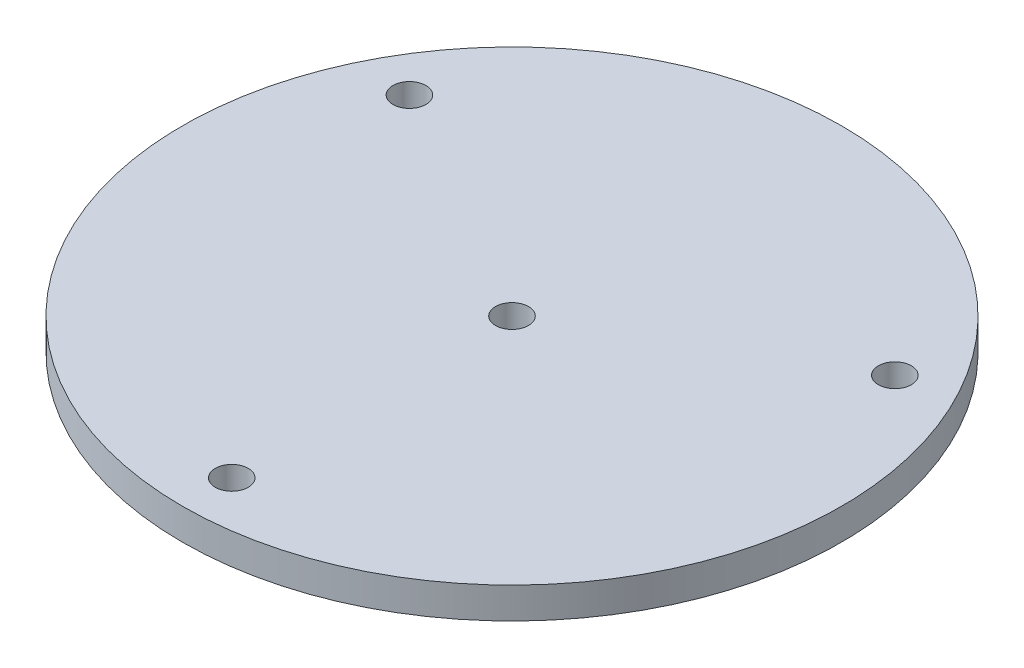
SolidWorks part; units mm, degrees
ref_plane "Front Plane" through (0, 0, 0) normal (0, 0, 1) x (1, 0, 0)
ref_plane "Top Plane" through (0, 0, 0) normal (0, 1, 0) x (1, 0, 0)
ref_plane "Right Plane" through (0, 0, 0) normal (1, 0, 0) x (0, 0, -1)
sketch "Sketch1" plane through (0, 0, 0) normal (0, 1, 0) x (1, 0, 0)
  line L0 (0, -44.5008) -> (0, -63.5) construction
  circle A0 centre (0, 0) radius 63.5
  circle A1 centre (0, 0) radius 3.175
  circle A2 centre (0, -54.0004) radius 3.175
  circle A3 centre (-46.7657, 27.0002) radius 3.175
  circle A4 centre (46.7657, 27.0002) radius 3.175
  point P14 (0, 0)
  dimension "D1" = 127
  dimension "D2" = 6.35
  dimension "D3" = 6.35
  dimension "D4" = 54.0004
  dimension "D5" = 3
extrude "Boss-Extrude1" add sketch "Sketch1" along normal blind 6 contours A1
